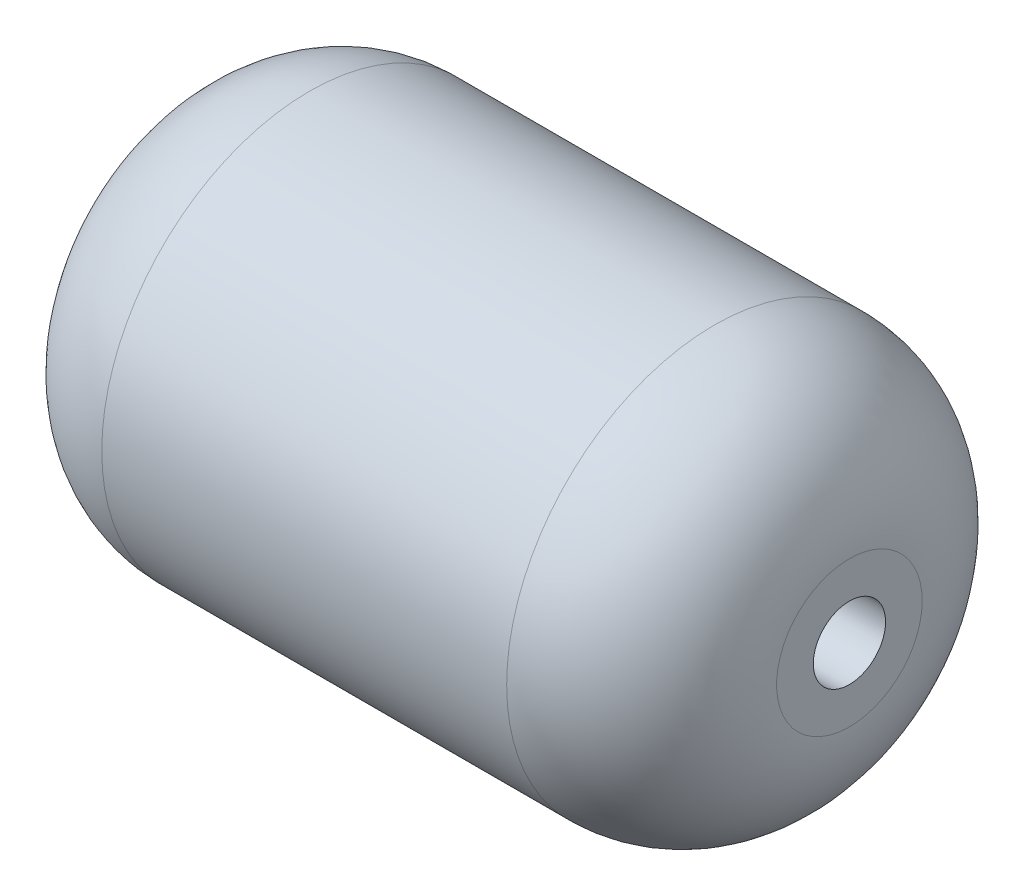
SolidWorks part; units mm, degrees
ref_plane "Plan de face" through (0, 0, 0) normal (0, 0, 1) x (1, 0, 0)
ref_plane "Plan de dessus" through (0, 0, 0) normal (0, 1, 0) x (1, 0, 0)
ref_plane "Plan de droite" through (0, 0, 0) normal (1, 0, 0) x (0, 0, -1)
sketch "Sketch1" plane through (0, 0, 0) normal (0, 0, 1) x (1, 0, 0)
  line L0 (-100, 21.5791) -> (-100, 10.7071)
  line L1 (-100, 10.7071) -> (100, 10.7071)
  line L2 (-60, 61.5791) -> (60, 61.5791)
  line L3 (0, 10.7071) -> (0, 0) construction
  line L4 (100, 21.5791) -> (100, 10.7071)
  line L5 (0, 0) -> (-39.5638, 0) construction
  line L6 (0, 10.7071) -> (0, 0) construction
  line L7 (-97.46, 21.5791) -> (-97.46, 13.2471)
  line L8 (-97.46, 13.2471) -> (97.46, 13.2471)
  line L9 (97.46, 21.5791) -> (97.46, 13.2471)
  line L10 (-60, 59.0391) -> (60, 59.0391)
  arc A0 (60, 61.5791) -> (100, 21.5791) centre (60, 21.5791) cw
  arc A1 (-60, 61.5791) -> (-100, 21.5791) centre (-60, 21.5791) ccw
  arc A2 (-60, 59.0391) -> (-97.46, 21.5791) centre (-60, 21.5791) ccw
  arc A3 (60, 59.0391) -> (97.46, 21.5791) centre (60, 21.5791) cw
  point P10 (0, 61.5791)
  point P11 (-19.7819, 0)
  dimension "D1" = 60
  dimension "D2" = 21.5791
  dimension "D3" = 10.7071
  dimension "D4" = 200
  dimension "D5" = 2.54
revolve "Revolve1" add sketch "Sketch1" angle 360 about L5
equation "\"Cout/Uni\"= ( ( \"Coût Achat\" + \"Coût Modif\" ) / \"Nb/Paquet\" )"
